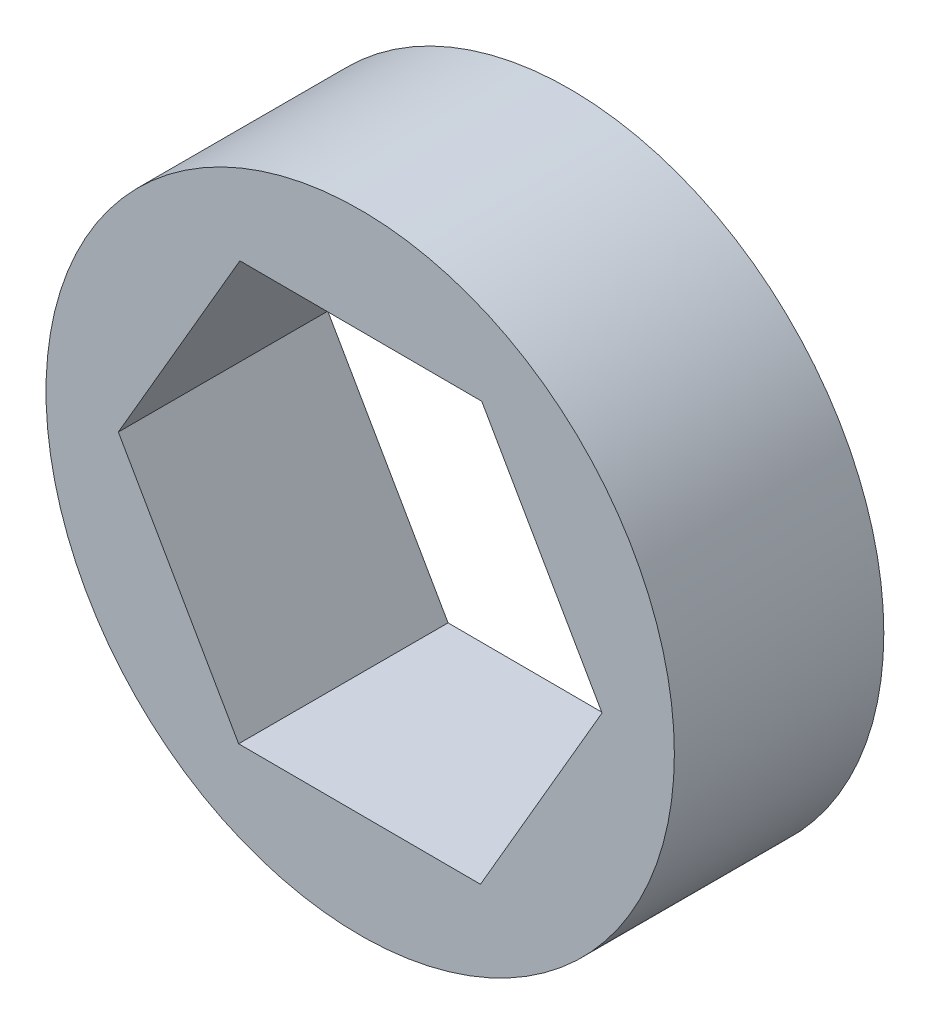
SolidWorks part; units mm, degrees
material "PET"
ref_plane "Front Plane" through (0, 0, 0) normal (0, 0, 1) x (1, 0, 0)
ref_plane "Top Plane" through (0, 0, 0) normal (0, 1, 0) x (1, 0, 0)
ref_plane "Right Plane" through (0, 0, 0) normal (1, 0, 0) x (0, 0, -1)
sketch "Sketch1" plane through (0, 0, 0) normal (0, 0, 1) x (1, 0, 0)
  line L1 (3.647, -6.361) -> (7.3323, -0.0221)
  line L2 (7.3323, -0.0221) -> (3.6853, 6.3389)
  line L3 (3.6853, 6.3389) -> (-3.647, 6.361)
  line L4 (-3.647, 6.361) -> (-7.3323, 0.0221)
  line L5 (-7.3323, 0.0221) -> (-3.6853, -6.3389)
  line L6 (-3.6853, -6.3389) -> (3.647, -6.361)
  circle A0 centre (0, 0) radius 9.525
  circle A1 centre (0, 0) radius 6.35 construction
  dimension "D1" = 19.05
  dimension "D2" = 12.7
extrude "Boss-Extrude1" add sketch "Sketch1" along normal blind 6.35
